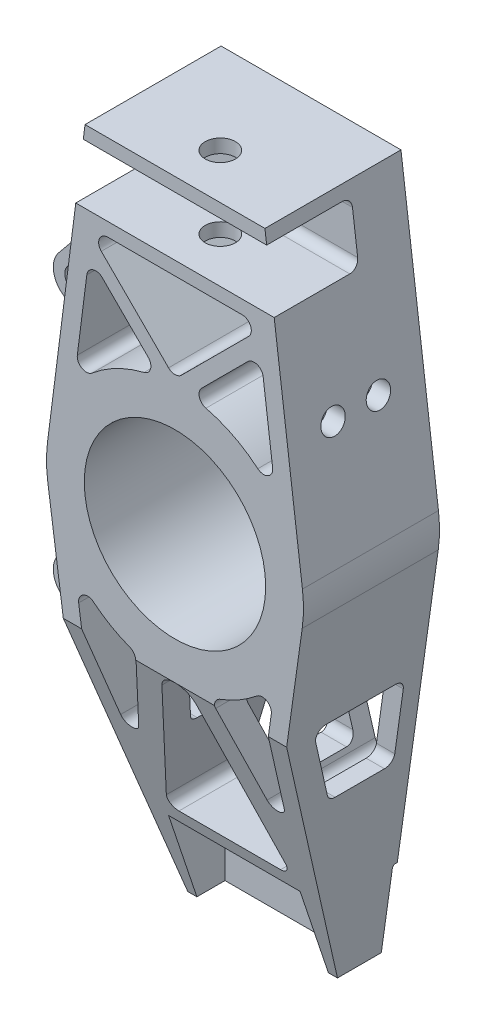
SolidWorks part; units mm, degrees
ref_plane "Front Plane" through (0, 0, 0) normal (0, 0, 1) x (1, 0, 0)
ref_plane "Top Plane" through (0, 0, 0) normal (0, 1, 0) x (1, 0, 0)
ref_plane "Right Plane" through (0, 0, 0) normal (1, 0, 0) x (0, 0, -1)
sketch "Sketch1" plane through (0, 0, 0) normal (0, 0, 1) x (1, 0, 0)
  line L0 (-29.75, 102.5) -> (-42.1573, 5.386)
  line L1 (-29.75, 102.5) -> (29.75, 102.5)
  line L3 (-24.75, -129.2275) -> (24.75, -129.2275)
  line L5 (0, 185.9794) -> (0, -218.2412) construction
  line L6 (29.75, 102.5) -> (42.1573, 5.386)
  line L7 (-30.3249, 98) -> (30.3249, 98) construction
  line L8 (-24.75, -129.2275) -> (-30.1796, -90.6073)
  line L9 (24.75, -129.2275) -> (42.0861, -5.9168)
  line L10 (-31.858, -35.5713) -> (-27.0621, -69.6844)
  line L11 (31.858, -35.5713) -> (27.0621, -69.6844)
  line L12 (-29.1615, 59.7616) -> (-32.3037, 35.167)
  line L13 (29.1615, 59.7616) -> (32.3037, 35.167)
  line L14 (-32.8163, 78.5) -> (32.8163, 78.5) construction
  line L15 (-22.2479, 74) -> (22.2479, 74)
  line L16 (-24.3693, 68.8787) -> (-2.1213, 46.6307)
  line L17 (2.1213, 46.6307) -> (24.3693, 68.8787)
  line L18 (-24.0644, 61.5027) -> (-8.8423, 46.2807)
  line L19 (24.0644, 61.5027) -> (8.8423, 46.2807)
  line L20 (-21.2199, -70.1355) -> (-13.1477, -43.4556)
  line L21 (21.2199, -70.1355) -> (13.1477, -43.4556)
  line L22 (-16.8181, -96.7275) -> (16.8181, -96.7275)
  line L23 (19.6896, -92.8587) -> (5.7429, -46.7625)
  line L24 (-5.7429, -46.7625) -> (-19.6896, -92.8587)
  line L29 (-37.8367, -36.1429) -> (-42.0861, -5.9168)
  line L30 (-30.1796, -90.6073) -> (-37.8367, -36.1429)
  line L31 (0.0039, -42.5) -> (132.5634, -42.5868) construction
  line L32 (-0.0039, -42.5) -> (-132.5634, -42.5868) construction
  arc A0 (-42.1573, 5.386) -> (-42.0861, -5.9168) centre (0, 0) ccw
  circle A1 centre (0, 0) radius 30
  arc A2 (22.2479, 74) -> (24.3693, 68.8787) centre (22.2479, 71) cw
  arc A3 (-22.2479, 74) -> (-24.3693, 68.8787) centre (-22.2479, 71) ccw
  arc A4 (29.1615, 59.7616) -> (24.0644, 61.5027) centre (26.1857, 59.3814) ccw
  arc A5 (-29.1615, 59.7616) -> (-24.0644, 61.5027) centre (-26.1857, 59.3814) cw
  arc A6 (27.3942, 32.4932) -> (10.2408, 41.2477) centre (0, 0) ccw
  arc A7 (-32.3037, 35.167) -> (-27.3942, 32.4932) centre (-29.3279, 34.7868) ccw
  arc A8 (32.3037, 35.167) -> (27.3942, 32.4932) centre (29.3279, 34.7868) cw
  arc A9 (-10.2408, 41.2477) -> (-27.3942, 32.4932) centre (0, 0) ccw
  arc A10 (-2.1213, 46.6307) -> (2.1213, 46.6307) centre (0, 48.7521) ccw
  arc A11 (8.8423, 46.2807) -> (10.2408, 41.2477) centre (10.9636, 44.1594) ccw
  arc A12 (-8.8423, 46.2807) -> (-10.2408, 41.2477) centre (-10.9636, 44.1594) cw
  arc A13 (5.7429, -46.7625) -> (-5.7429, -46.7625) centre (0, -48.5) ccw
  arc A14 (27.0621, -69.6844) -> (21.2199, -70.1355) centre (24.0913, -69.2667) cw
  arc A15 (-27.0621, -69.6844) -> (-21.2199, -70.1355) centre (-24.0913, -69.2667) ccw
  arc A16 (-26.9826, -32.8358) -> (-14.963, -39.7789) centre (0, 0) ccw
  arc A17 (42.0861, -5.9168) -> (42.1573, 5.386) centre (0, 0) ccw
  arc A18 (31.858, -35.5713) -> (26.9826, -32.8358) centre (28.8872, -35.1536) ccw
  arc A19 (-31.858, -35.5713) -> (-26.9826, -32.8358) centre (-28.8872, -35.1536) cw
  arc A20 (14.963, -39.7789) -> (26.9826, -32.8358) centre (0, 0) ccw
  arc A21 (13.1477, -43.4556) -> (14.963, -39.7789) centre (16.0192, -42.5868) cw
  arc A22 (-13.1477, -43.4556) -> (-14.963, -39.7789) centre (-16.0192, -42.5868) ccw
  arc A23 (16.8181, -96.7275) -> (19.6896, -92.8587) centre (16.8181, -93.7275) ccw
  arc A24 (-16.8181, -96.7275) -> (-19.6896, -92.8587) centre (-16.8181, -93.7275) cw
  circle A32 centre (-12, -115.2275) radius 3
  circle A33 centre (12, -115.2275) radius 3
  point P8 (0, 102.5)
  point P17 (0, -129.2275)
  point P34 (0, 74)
  point P45 (28.3868, 65.8252)
  point P48 (-28.3868, 65.8252)
  point P50 (-33.4466, 26.2217)
  point P53 (33.4466, 26.2217)
  point P56 (0, 44.5094)
  point P59 (4.7908, 42.2291)
  point P62 (-4.7908, 42.2291)
  point P65 (0, -27.7811)
  point P68 (25.1653, -83.176)
  point P71 (-25.1653, -83.176)
  point P74 (33.1135, -26.641)
  point P77 (-33.1135, -26.641)
  point P80 (12.3076, -40.6789)
  point P83 (-12.3076, -40.6789)
  point P85 (-36.9395, -42.5242)
  point P90 (-30.1796, -90.6073)
  point P98 (0, -30)
  point P101 (0, 0)
  point P105 (-30.9547, -85.0941)
  point P108 (-33.4499, 73.5403)
  dimension "D1" = 85
  dimension "D2" = 60
  dimension "D13" = 3
  dimension "D14" = 3
  dimension "D15" = 3
  dimension "D16" = 3
  dimension "D17" = 3
  dimension "D19" = 6
  dimension "D20" = 3
  dimension "D21" = 3
  dimension "D22" = 3
  dimension "D24" = 3
  dimension "D25" = 46.0963
  dimension "D28" = 6
  dimension "D30" = 24
  dimension "D3" = 102.5
  dimension "D4" = 59.5
  dimension "D5" = 4.5
  dimension "D6" = 49.5
  dimension "D7" = 123.3107
  dimension "D8" = 6
  dimension "D9" = 6
  dimension "D10" = 19.5
  dimension "D11" = 4.5
  dimension "D12" = 5
  dimension "D18" = 15.2221
  dimension "D23" = 32.5
  dimension "D26" = 39
  dimension "D27" = 55
  dimension "D29" = 14
  dimension "D35" = 5
extrude "Boss-Extrude1" add sketch "Sketch1" along normal mid plane 45
sketch "Sketch2" plane through (0, 0, 22.5) normal (0, 0, 1) x (1, 0, 0)
  line L0 (-24.75, -129.2275) -> (24.75, -129.2275) construction
  line L1 (-21.75, -101.2275) -> (21.75, -101.2275)
  line L2 (-21.75, -101.2275) -> (-21.75, -129.2275)
  line L3 (-21.75, -129.2275) -> (21.75, -129.2275)
  line L4 (21.75, -101.2275) -> (21.75, -129.2275)
  line L5 (0, 185.9794) -> (0, -218.2412) construction
  line L6 (-16.8181, -96.7275) -> (16.8181, -96.7275) construction
  point P6 (0, -129.2275)
  dimension "D3" = 28
  dimension "D1" = 43.5
  dimension "D2" = 4.5
extrude "Cut-Extrude1" cut sketch "Sketch2" against normal blind 45 from offset 6.7
sketch "Sketch6" plane through (0, 0, 0) normal (1, 0, 0) x (0, 0, -1)
  line L0 (22.5, -5.9168) -> (22.5, -129.2275) construction
  line L1 (22.5, -102.2275) -> (22, -102.2275)
  line L2 (22.5, -102.2275) -> (22.5, -129.2275)
  line L3 (22.5, -129.2275) -> (21, -129.2275)
  line L4 (21, -103.2275) -> (21, -129.2275)
  line L5 (-22.5, -129.2275) -> (22.5, -129.2275) construction
  line L6 (21, -129.2275) -> (6.5, -129.2275) construction
  line L7 (6.5, -129.2275) -> (-22.5, -42.5242)
  line L8 (-22.5, -5.9168) -> (-22.5, -129.2275) construction
  line L9 (-22.5, -42.5242) -> (-22.5, -129.2275)
  line L10 (-22.5, -101.2275) -> (-22.5, -129.2275) construction
  line L11 (-22.5, -129.2275) -> (6.5, -129.2275)
  line L12 (-22.5, 98) -> (2.5, 98)
  line L13 (-22.5, 5.386) -> (-22.5, 102.5) construction
  line L14 (5.5, 95) -> (5.5, 81.5)
  line L15 (-22.5, 78.5) -> (2.5, 78.5)
  line L16 (-22.5, 78.5) -> (-22.5, 98)
  line L17 (-22.5, 102.5) -> (22.5, 102.5) construction
  arc A1 (5.5, 81.5) -> (2.5, 78.5) centre (2.5, 81.5) cw
  arc A2 (2.5, 98) -> (5.5, 95) centre (2.5, 95) cw
  arc A3 (22, -102.2275) -> (21, -103.2275) centre (22, -103.2275) ccw
  point P10 (22.5, -102.2275)
  point P28 (5.5, 78.5)
  point P31 (5.5, 98)
  dimension "D3" = 1
  dimension "D10" = 3
  dimension "D1" = 1.5
  dimension "D2" = 27
  dimension "D4" = 14.5
  dimension "D5" = 86.7033
  dimension "D6" = 4.5
  dimension "D7" = 28
  dimension "D8" = 28
  dimension "D9" = 19.5
extrude "Cut-Extrude3" cut sketch "Sketch6" against normal through all both and the other way through all
sketch "Sketch7" plane through (0, 102.5, 0) normal (0, 1, 0) x (1, 0, 0)
  line L0 (-21.75, -22.5) -> (21.75, -22.5) construction
  circle A0 centre (0, -7.5) radius 5
  dimension "D1" = 10
  dimension "D2" = 15
extrude "Cut-Extrude4" cut sketch "Sketch7" against normal up to surface (28.5 mm away) up to face at (0, 74, 0)
sketch "Sketch8" plane through (0, 0, 0) normal (1, 0, 0) x (0, 0, -1)
  line L0 (-9.5, -42.5242) -> (13.5, -42.5242)
  line L1 (16.5, -45.5242) -> (16.5, -65.5242)
  line L2 (13.5, -68.5242) -> (-2.8105, -68.5242)
  line L3 (-5.6556, -66.4758) -> (-12.3451, -46.4758)
  line L4 (22.5, -102.2275) -> (22.5, -5.9168) construction
  line L5 (-22.5, -42.5242) -> (6.5, -129.2275) construction
  arc A0 (-2.8105, -68.5242) -> (-5.6556, -66.4758) centre (-2.8105, -65.5242) cw
  arc A1 (16.5, -65.5242) -> (13.5, -68.5242) centre (13.5, -65.5242) cw
  arc A2 (13.5, -42.5242) -> (16.5, -45.5242) centre (13.5, -45.5242) cw
  arc A3 (-9.5, -42.5242) -> (-12.3451, -46.4758) centre (-9.5, -45.5242) ccw
  dimension "D1" = 3
  dimension "D2" = 23
  dimension "D3" = 20
  dimension "D4" = 6
extrude "Cut-Extrude5" cut sketch "Sketch8" against normal up to surface and the other way through all up to face at (-29.7442, -50.6071, 2.6831)
sketch "Sketch10" plane through (0, 0, 0) normal (1, 0, 0) x (0, 0, -1)
  line L0 (-7.5, 43.5) -> (7.5, 43.5) construction
  line L1 (2.5, 78.5) -> (-22.5, 78.5) construction
  circle A0 centre (-7.5, 43.5) radius 4
  circle A1 centre (-7.5, 43.5) radius 4
  circle A2 centre (7.5, 43.5) radius 4
  point P8 (0, 43.5)
  dimension "D1" = 8
  dimension "D2" = 15
  dimension "D3" = 35
extrude "Cut-Extrude6" cut sketch "Sketch10" along normal through all from surface contours A2 | A0
ref_plane "Plane1" through (0, 0, -4.1) normal (0, 0, 1) x (1, 0, 0)
sketch "Sketch12" plane through (0, 0, -4.1) normal (0, 0, 1) x (1, 0, 0)
  line L0 (-30.1796, -90.6073) -> (-37.8367, -36.1429) construction
  line L1 (-30.3188, -89.617) -> (-63.9208, -62.786)
  line L2 (-38.168, -33.7861) -> (-63.3094, -50.154)
  line L3 (-59.0538, -84.6382) -> (-59.0538, 139.5785) construction
  line L4 (-37.8367, -36.1429) -> (-42.0861, -5.9168) construction
  line L5 (-29.75, 102.5) -> (-42.1573, 5.386) construction
  line L6 (-38.168, -33.7861) -> (-36.5057, -45.6102)
  line L10 (-32.3586, -75.1083) -> (-30.3188, -89.617)
  line L11 (-51.041, -49.3263) -> (-41.1344, -42.8768)
  line L12 (-51.7896, -64.7946) -> (-37.0867, -76.5348)
  line L13 (0, 185.9794) -> (0, -218.2412) construction
  line L14 (-33.4551, 73.5) -> (-65.0936, 34.7831)
  line L15 (-41.4898, 10.6112) -> (-62.9747, 23.1046)
  line L16 (-53.656, 39.2975) -> (-41.5168, 54.1525)
  line L18 (-44.5749, 19.3459) -> (-50.6802, 22.896)
  line L19 (-33.4551, 73.5) -> (-36.218, 51.874)
  line L20 (-41.4898, 10.6112) -> (-40.0911, 21.5591)
  arc A0 (-63.3094, -50.154) -> (-63.9208, -62.786) centre (-59.0538, -56.6908) ccw
  arc A1 (-65.0936, 34.7831) -> (-62.9747, 23.1046) centre (-59.0538, 29.8475) ccw
  arc A3 (-41.1344, -42.8768) -> (-36.5057, -45.6102) centre (-39.4977, -45.391) cw
  arc A4 (-37.0867, -76.5348) -> (-32.3586, -75.1083) centre (-35.2147, -74.1905) ccw
  circle A5 centre (-59.0538, -56.6908) radius 7.8 construction
  arc A6 (-52.0846, -53.1878) -> (-52.4555, -60.8504) centre (-59.0538, -56.6908) cw
  arc A7 (-51.7896, -64.7946) -> (-52.4555, -60.8504) centre (-49.9177, -62.4503) cw
  arc A8 (-51.041, -49.3263) -> (-52.0846, -53.1878) centre (-49.4042, -51.8405) ccw
  circle A9 centre (-59.0538, -56.6908) radius 4
  arc A10 (-51.917, 26.7) -> (-53.4776, 35.3015) centre (-59.0538, 29.8475) ccw
  arc A11 (-59.0538, 37.6475) -> (-59.0538, 22.0475) centre (-59.0538, 29.8475) ccw construction
  arc A12 (-50.6802, 22.896) -> (-51.917, 26.7) centre (-49.1721, 25.4894) cw
  arc A13 (-53.656, 39.2975) -> (-53.4776, 35.3015) centre (-51.333, 37.3992) ccw
  arc A14 (-40.0911, 21.5591) -> (-44.5749, 19.3459) centre (-43.0669, 21.9393) cw
  arc A15 (-41.5168, 54.1525) -> (-36.218, 51.874) centre (-39.1938, 52.2542) cw
  circle A16 centre (-59.0538, 29.8475) radius 4
  point P0 (-30.3188, -89.617)
  point P1 (-38.168, -33.7861)
  point P6 (-24.75, -129.2275)
  point P12 (-33.4551, 73.5)
  point P15 (-41.4898, 10.6112)
  point P33 (-54.2462, -62.833)
  point P36 (-53.6755, -51.0415)
  point P42 (-52.2323, 16.8579)
  point P50 (-49.2743, 54.1415)
  point P51 (-132.477, 21.7774)
  point P53 (0, 0)
  point P61 (-40.6643, 17.0719)
  point P64 (-34.891, 62.2607)
  point P66 (0, 0)
  point P67 (0, 0)
  dimension "D4" = 40
  dimension "D5" = 15.6
  dimension "D6" = 56.38
  dimension "D9" = 3
  dimension "D10" = 3
  dimension "D11" = 3
  dimension "D13" = 8
  dimension "D19" = 3
  dimension "D20" = 3
  dimension "D21" = 8
  dimension "D22" = 3
  dimension "D2" = 43
  dimension "D3" = 30
  dimension "D7" = 6
  dimension "D8" = 6
  dimension "D12" = 59.0538
  dimension "D14" = 5
  dimension "D15" = 63.4
  dimension "D16" = 50
  dimension "D17" = 6
  dimension "D18" = 6
  dimension "D23" = 7.0624
extrude "Boss-Extrude2" add sketch "Sketch12" against normal blind 10 contours A8 L11 A3 L6 L2 A0 L1 L10 A4 L12 A7 A6 A9 | L16 A15 L19 L14 A1 L15 L20 A14 L18 A12 A10 A13 A16
